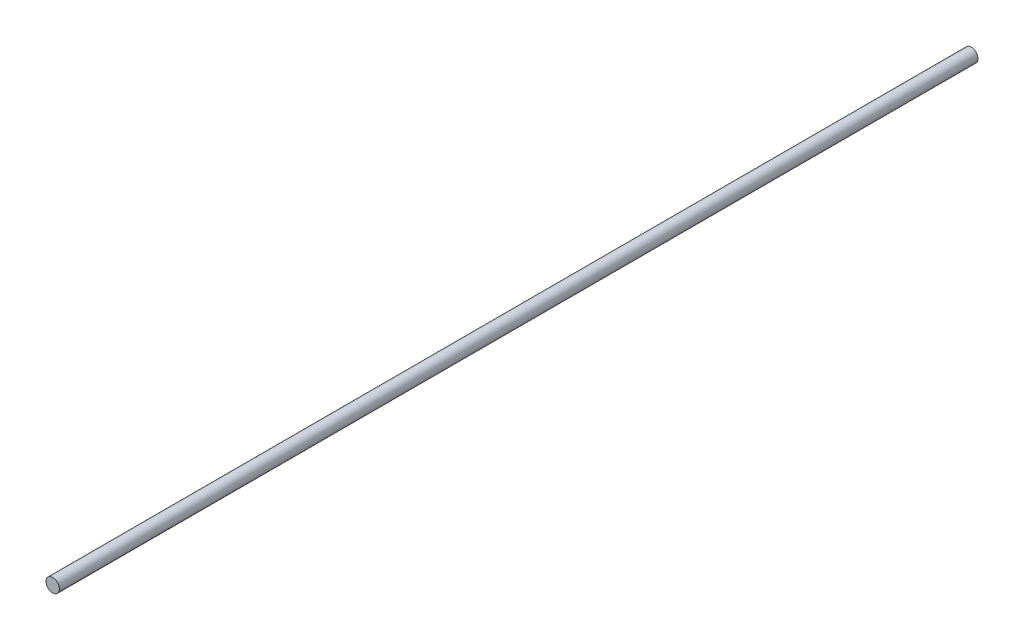
SolidWorks part; units mm, degrees
material "Chrome Stainless Steel"
ref_plane "Front Plane" through (0, 0, 0) normal (0, 0, 1) x (1, 0, 0)
ref_plane "Top Plane" through (0, 0, 0) normal (0, 1, 0) x (1, 0, 0)
ref_plane "Right Plane" through (0, 0, 0) normal (1, 0, 0) x (0, 0, -1)
sketch "Sketch1" plane through (0, 0, 0) normal (0, 0, 1) x (1, 0, 0)
  circle A0 centre (0, 0) radius 4
  dimension "D1" = 8
extrude "Boss-Extrude1" add sketch "Sketch1" along normal blind 550
